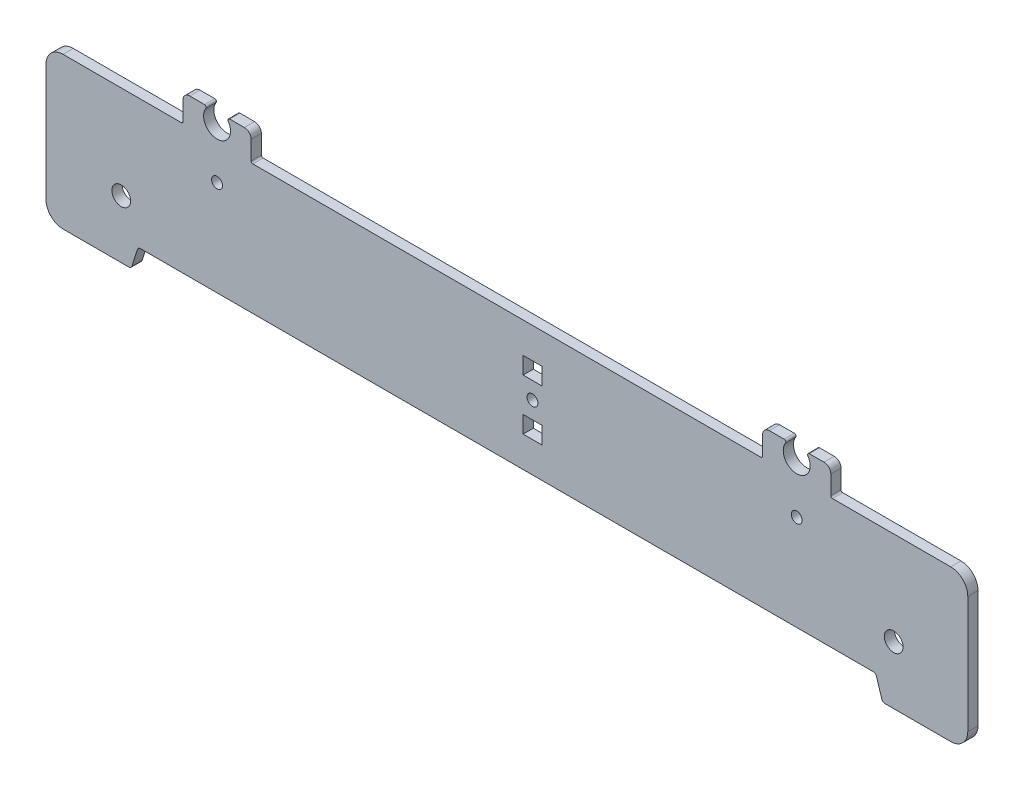
SolidWorks part; units mm, degrees
ref_plane "Alzado" through (0, 0, 0) normal (0, 0, 1) x (1, 0, 0)
ref_plane "Planta" through (0, 0, 0) normal (0, 1, 0) x (1, 0, 0)
ref_plane "Vista lateral" through (0, 0, 0) normal (1, 0, 0) x (0, 0, -1)
sketch "Model" plane through (0, 0, 0) normal (0, 0, 1) x (1, 0, 0)
  line L0 (136.1313, 8.1726) -> (28.6911, 8.1751)
  line L1 (27.7368, 7.4739) -> (26.1759, 2.4887)
  line L2 (25.2215, 1.7875) -> (5.9563, 1.7875)
  line L3 (0.9563, 6.7875) -> (0.9563, 41.1751)
  line L4 (5.9563, 46.1751) -> (10.9563, 46.1751)
  line L5 (10.9563, 46.1751) -> (40.6288, 46.1751)
  line L6 (41.1288, 46.6751) -> (41.1288, 52.1731)
  line L7 (43.1288, 54.1731) -> (47.445, 54.1731)
  line L8 (54.8127, 54.1731) -> (59.1288, 54.1731)
  line L9 (61.1288, 52.1731) -> (61.1288, 46.6751)
  line L10 (61.6288, 46.1751) -> (136.1313, 46.1751)
  line L11 (136.1313, 46.1751) -> (210.6338, 46.1751)
  line L12 (211.1338, 46.6751) -> (211.1338, 52.1731)
  line L13 (213.1338, 54.1731) -> (217.45, 54.1731)
  line L14 (224.8177, 54.1731) -> (229.1338, 54.1731)
  line L15 (231.1338, 52.1731) -> (231.1338, 46.6751)
  line L16 (231.6338, 46.1751) -> (261.3063, 46.1751)
  line L17 (261.3063, 46.1751) -> (266.3063, 46.1751)
  line L18 (271.3063, 41.1751) -> (271.3063, 6.7875)
  line L19 (266.3063, 1.7875) -> (247.0411, 1.7875)
  line L20 (246.0868, 2.4887) -> (244.5259, 7.4739)
  line L21 (243.5715, 8.1751) -> (136.1313, 8.1726)
  line L22 (140.8813, 37.1739) -> (140.8813, 32.1739)
  line L23 (140.8813, 37.1739) -> (146.3813, 37.1739)
  line L24 (146.3813, 37.1739) -> (146.3813, 32.1739)
  line L25 (140.8813, 17.1739) -> (140.8813, 22.1739)
  line L26 (140.8813, 17.1739) -> (146.3813, 17.1739)
  line L27 (146.3813, 17.1739) -> (146.3813, 22.1739)
  line L28 (140.8813, 32.1739) -> (146.3813, 32.1739)
  line L29 (140.8813, 22.1739) -> (146.3813, 22.1739)
  circle A0 centre (51.1288, 36.1767) radius 1.6
  circle A1 centre (221.1338, 36.1767) radius 1.6
  circle A2 centre (143.6313, 27.1739) radius 1.6
  circle A3 centre (23.0172, 18.7875) radius 2.75
  circle A4 centre (249.5754, 18.7875) radius 2.75
  arc A5 (28.6911, 8.1751) -> (27.7368, 7.4739) centre (28.6911, 7.1751) ccw
  arc A6 (25.2215, 1.7875) -> (26.1759, 2.4887) centre (25.2215, 2.7875) ccw
  arc A7 (0.9563, 6.7875) -> (5.9563, 1.7875) centre (5.9563, 6.7875) ccw
  arc A8 (5.9563, 46.1751) -> (0.9563, 41.1751) centre (5.9563, 41.1751) ccw
  arc A9 (40.6288, 46.1751) -> (41.1288, 46.6751) centre (40.6288, 46.6751) ccw
  arc A10 (43.1288, 54.1731) -> (41.1288, 52.1731) centre (43.1288, 52.1731) ccw
  arc A11 (47.8589, 53.3926) -> (47.445, 54.1731) centre (47.445, 53.6731) ccw
  arc A12 (47.8589, 53.3926) -> (54.3987, 53.3926) centre (51.1288, 51.1767) ccw
  arc A13 (54.8127, 54.1731) -> (54.3987, 53.3926) centre (54.8127, 53.6731) ccw
  arc A14 (61.1288, 52.1731) -> (59.1288, 54.1731) centre (59.1288, 52.1731) ccw
  arc A15 (61.1288, 46.6751) -> (61.6288, 46.1751) centre (61.6288, 46.6751) ccw
  arc A16 (210.6338, 46.1751) -> (211.1338, 46.6751) centre (210.6338, 46.6751) ccw
  arc A17 (213.1338, 54.1731) -> (211.1338, 52.1731) centre (213.1338, 52.1731) ccw
  arc A18 (217.8639, 53.3926) -> (217.45, 54.1731) centre (217.45, 53.6731) ccw
  arc A19 (217.8639, 53.3926) -> (224.4037, 53.3926) centre (221.1338, 51.1767) ccw
  arc A20 (224.8177, 54.1731) -> (224.4037, 53.3926) centre (224.8177, 53.6731) ccw
  arc A21 (231.1338, 52.1731) -> (229.1338, 54.1731) centre (229.1338, 52.1731) ccw
  arc A22 (231.1338, 46.6751) -> (231.6338, 46.1751) centre (231.6338, 46.6751) ccw
  arc A23 (271.3063, 41.1751) -> (266.3063, 46.1751) centre (266.3063, 41.1751) ccw
  arc A24 (266.3063, 1.7875) -> (271.3063, 6.7875) centre (266.3063, 6.7875) ccw
  arc A25 (246.0868, 2.4887) -> (247.0411, 1.7875) centre (247.0411, 2.7875) ccw
  arc A26 (244.5259, 7.4739) -> (243.5715, 8.1751) centre (243.5715, 7.1751) ccw
extrude "Saliente-Extruir1" add sketch "Model" along normal blind 3
